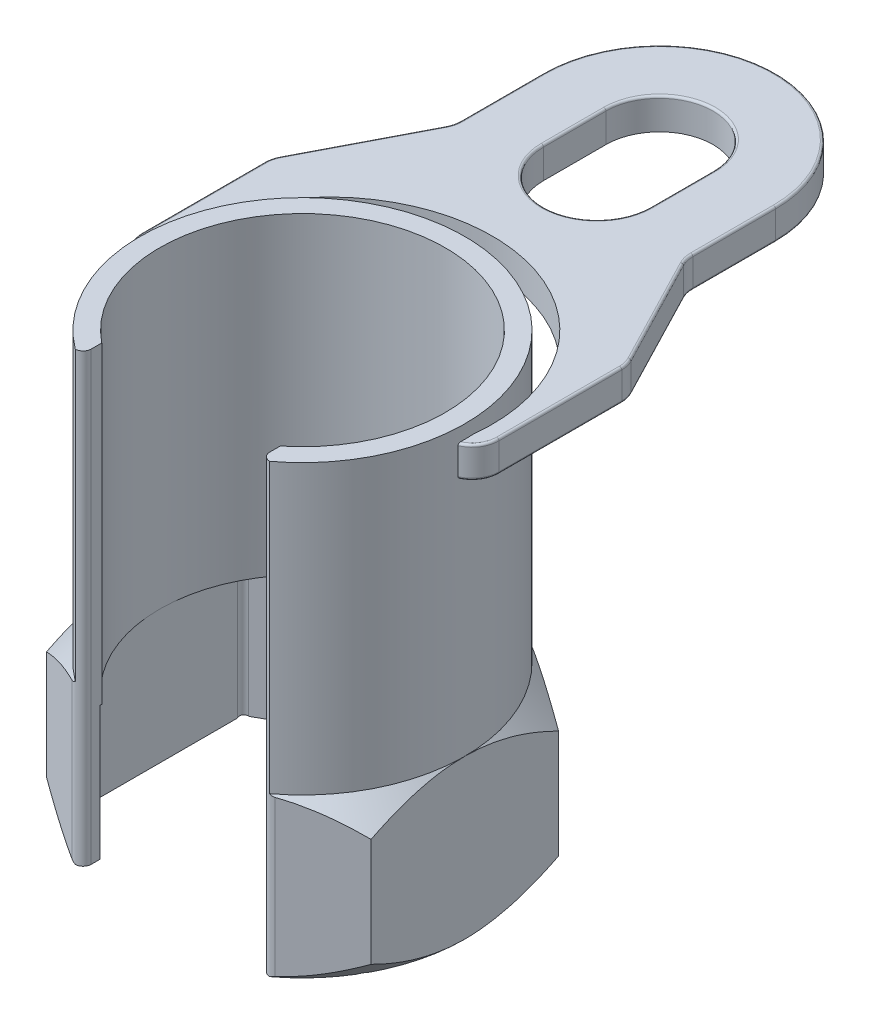
SolidWorks part; units mm, degrees
ref_plane "Front" through (0, 0, 0) normal (0, 0, 1) x (1, 0, 0)
ref_plane "Top" through (0, 0, 0) normal (0, 1, 0) x (1, 0, 0)
ref_plane "Right" through (0, 0, 0) normal (1, 0, 0) x (0, 0, -1)
sketch "Sketch1" plane through (0, 0, 0) normal (0, 1, 0) x (1, 0, 0)
  line L0 (-20, -24.98) -> (-20, -30.453)
  line L1 (0, 42) -> (-36.3731, 21)
  line L2 (0, 11.9615) -> (0, -7.933) construction
  line L3 (-36.3731, 21) -> (-36.3731, -21)
  line L4 (-36.3731, -21) -> (-20, -30.453)
  line L5 (20, -30.453) -> (36.3731, -21)
  line L6 (36.3731, -21) -> (36.3731, 21)
  line L7 (36.3731, 21) -> (0, 42)
  line L8 (20, -24.98) -> (20, -30.453)
  arc A0 (20, -30.3809) -> (-20, -30.3809) centre (0, 0) ccw construction
  arc A1 (20, -24.98) -> (-20, -24.98) centre (0, 0) ccw
  point P18 (-36.3731, -21)
  point P26 (36.3731, 21)
  dimension "D" = 84
  dimension "D2" = 64
  dimension "C" = 40
extrude "Extrude1" add sketch "Sketch1" along normal blind 35.5
sketch "Sketch3" plane through (0, 35.5, 0) normal (0, 1, 0) x (-1, 0, 0)
  line L0 (-36.3731, 21) -> (-36.3731, -21) construction
  line L2 (-20, 30.3808) -> (-20, 24.98)
  line L3 (20, 30.3808) -> (20, 24.98)
  arc A0 (-20, 24.98) -> (20, 24.98) centre (0, 0) ccw
  arc A1 (-20, 24.98) -> (20, 24.98) centre (0, 0) ccw construction
  arc A2 (-20, 30.3808) -> (20, 30.3808) centre (0, 0) ccw
  dimension "D1" = 0.0001
extrude "Extrude2" add sketch "Sketch3" along normal blind 64.5
sketch "Sketch8" plane through (0, 0, 0) normal (0, -1, 0) x (1, 0, 0)
  line L1 (36.3731, 21) -> (36.3731, -21) construction
  circle A0 centre (0, 0) radius 36.3731
extrude "Cut-Extrude4" cut sketch "Sketch8" against normal through all draft 45 flip side to cut
sketch "Sketch19" plane through (0, 35.5, 0) normal (0, 1, 0) x (-1, 0, 0)
  circle A1 centre (0, 0) radius 36.373
  arc A2 (-20, 30.3808) -> (20, 30.3808) centre (0, 0) ccw construction
extrude "Cut-Extrude6" cut sketch "Sketch19" against normal through all draft 45 flip side to cut
sketch "Sketch26" plane through (0, 0, 0) normal (0, -1, 0) x (1, 0, 0)
  line L1 (-32, -18.4752) -> (0, -36.9504)
  line L2 (0, -36.9504) -> (32, -18.4752)
  line L3 (32, -18.4752) -> (32, 18.4752)
  line L4 (32, 18.4752) -> (0, 36.9504)
  line L5 (0, 36.9504) -> (-32, 18.4752)
  line L6 (-32, 18.4752) -> (-32, -18.4752)
  circle A0 centre (0, 0) radius 32 construction
  dimension "D1" = 64
extrude "Cut-Extrude9" cut sketch "Sketch26" against normal up to vertex (38.5 mm away)
fillet "Fillet1" radius 1.8 7 edges at (-32, 15.2252, -18.4752) (-32, 15.2252, 18.4752) (32, 15.2252, 18.4752) (32, 15.2252, -18.4752) (-20, 17.7499, 30.453) (20, 17.7499, 30.453) (0, 15.2252, -36.9504)
sketch "Sketch4" [suppressed] plane through (0, 0, 0) normal (0, 1, 0) x (-1, 0, 0)
  line L0 (0, -11.2014) -> (0, 12.8888) construction
  line L1 (-10, -2.5) -> (10, -2.5)
  line L2 (-10, -2.5) -> (-10, 3.8)
  line L3 (-10, 3.8) -> (10, 3.8)
  line L4 (10, -2.5) -> (10, 3.8)
  line L5 (16.2585, 0) -> (-21.4153, 0) construction
  dimension "D1" = 64
  dimension "D2" = 11.5
  dimension "D3" = 10.2
sketch "Sketch12" [suppressed] plane through (0, 0, 0) normal (0, 1, 0) x (1, 0, 0)
  line L0 (-11, -4) -> (11, -4)
  line L1 (0, 0) -> (-11.4274, 0) construction
  line L2 (-11, 2.7) -> (11, 2.7)
  line L3 (-4.5, 14.3091) -> (4.5, 14.3091)
  line L4 (-7, 3.2909) -> (-7, -3.2909) construction
  line L5 (7, -3.2909) -> (7, 3.2909) construction
  arc A0 (-11, -4) -> (11, -4) centre (0, 0) ccw
  arc A1 (-6.3246, -3) -> (6.3246, -3) centre (0, 0) ccw construction
  arc A2 (-4.5, 14.3091) -> (-11, 2.7) centre (2.617, 2.7) ccw
  arc A3 (-4.5, 14.3091) -> (4.5, 14.3091) centre (0, 0) ccw construction
  arc A4 (4.5, 14.3091) -> (11, 2.7) centre (-2.617, 2.7) cw
ref_plane "Plane3" through (0, 90, 0) normal (0, 1, 0) x (-1, 0, 0)
sketch "Sketch16" plane through (0, 90, 0) normal (0, 1, 0) x (-1, 0, 0)
  line L5 (0, 0) -> (0, 54.2988) construction
  line L6 (-26, -80) -> (-26, -61.4631)
  line L10 (26, -61.4631) -> (26, -80)
  line L11 (39.3265, -34.2988) -> (26.6735, -58.7012)
  line L12 (-39.3265, -34.2988) -> (-26.6735, -58.7012)
  line L13 (-40, -4.024) -> (-40, -31.5369)
  line L14 (40, -4.024) -> (40, -31.5369)
  line L15 (38.3763, 1.5) -> (-38.1367, 1.5) construction
  arc A0 (-21.7747, 29.1351) -> (21.7747, 29.1351) centre (0, 0) ccw construction
  arc A1 (-36.342, 1.5) -> (36.342, 1.5) centre (0, 0) ccw
  arc A2 (40, -4.024) -> (36.342, 1.5) centre (34, -4.024) ccw
  arc A3 (-40, -4.024) -> (-36.342, 1.5) centre (-34, -4.024) cw
  arc A4 (-40, -31.5369) -> (-39.3265, -34.2988) centre (-34, -31.5369) ccw
  arc A5 (-26.6735, -58.7012) -> (-26, -61.4631) centre (-32, -61.4631) cw
  arc A7 (40, -31.5369) -> (39.3265, -34.2988) centre (34, -31.5369) cw
  arc A8 (26.6735, -58.7012) -> (26, -61.4631) centre (32, -61.4631) ccw
  arc A15 (26, -80) -> (-26, -80) centre (0, -80) cw
  point P18 (-40, -33)
  point P22 (-26, -60)
  point P25 (40, -33)
  point P30 (26, -60)
  dimension "D1" = 80
  dimension "D2" = 33
  dimension "D3" = 60
  dimension "D4" = 6
  dimension "D6" = 52
  dimension "D7" = 80
  dimension "D14" = 1.5
extrude "Extrude7" add sketch "Sketch16" along normal blind 7
sketch "Sketch25" plane through (0, 97, 0) normal (0, -1, 0) x (1, 0, 0)
  line L1 (-29.4486, 0) -> (37.9585, 0) construction
  line L3 (0, -57.3769) -> (0, 10.8445) construction
  line L4 (-12, -80) -> (-12, -66)
  line L5 (12, -80) -> (12, -66)
  arc A0 (-21.7747, 29.1351) -> (21.7747, 29.1351) centre (0, 0) ccw construction
  arc A2 (-26, -80) -> (26, -80) centre (0, -80) ccw construction
  arc A6 (36.3179, -2) -> (-36.3179, -2) centre (0, 0) cw
  arc A7 (36.3179, -2) -> (-36.3179, -2) centre (0, -6) cw
  arc A8 (12, -80) -> (-12, -80) centre (0, -80) cw
  arc A9 (12, -66) -> (-12, -66) centre (0, -66) ccw
  dimension "D1" = 40
  dimension "D2" = 24
  dimension "D3" = 2
  dimension "D4" = 6
extrude "Cut-Extrude8" cut sketch "Sketch25" along normal up to next
fillet "Fillet4" radius 0.5 30 edges at (12, 97, -73) (0, 97, -92) (-12, 97, -73) (39.0026, 97, -0.7113) (40, 97, -17.7805) (39.8292, 97, -32.9584) (-39.0026, 97, -0.7113) (-40, 97, -17.7805) (-39.8292, 97, -32.9584) (-33, 97, -46.5) (-26.1708, 97, -60.0416) (-26, 97, -70.7315) (0, 97, -106) (26, 97, -70.7315) (26.1708, 97, -60.0416) (39.0026, 90, -0.7113) (40, 90, -17.7805) (39.8292, 90, -32.9584) (-39.0026, 90, -0.7113) (-40, 90, -17.7805) (-39.8292, 90, -32.9584) (-33, 90, -46.5) (-26.1708, 90, -60.0416) (-26, 90, -70.7315) (0, 90, -106) (26, 90, -70.7315) (26.1708, 90, -60.0416) (0, 97, -54) (33, 97, -46.5) (33, 90, -46.5)
sketch "Sketch20" [suppressed] plane through (0, 0, 0) normal (0, 1, 0) x (1, 0, 0)
  line L0 (0, 0) -> (0, 12.8849) construction
  line L1 (-7.5, -9.3675) -> (-7.5, -14.4157)
  line L2 (7.5, -9.3675) -> (7.5, -14.4157)
  arc A0 (7.5, -14.4157) -> (-7.5, -14.4157) centre (0, 0) ccw
  arc A1 (7.5, -9.3675) -> (-7.5, -9.3675) centre (0, 0) ccw
  circle A2 centre (0, 0) radius 16.25 construction
  circle A3 centre (0, 0) radius 12 construction
  dimension "D1" = 84
  dimension "D2" = 64
  dimension "D3" = 40
extrude "Extrude3" [suppressed] add sketch "Sketch20" along normal blind 70
ref_plane "Plane7" [suppressed] through (0, 41.999, 0) normal (0, 1, 0) x (-1, 0, 0)
sketch "Sketch21" [suppressed] plane through (0, 41.999, 0) normal (0, 1, 0) x (-1, 0, 0)
  line L1 (2.5, 16.0565) -> (2.5, 19.8734)
  line L2 (7.5, 14.4157) -> (7.5, 9.3675) construction
  line L4 (7.5, 14.4157) -> (7.5, 18.5729)
  arc A1 (2.5, 16.0565) -> (7.5, 14.4157) centre (0, 0) ccw
  arc A2 (2.5, 19.8734) -> (7.5, 18.5729) centre (0, 0) ccw
  arc A3 (-7.5, 14.4157) -> (7.5, 14.4157) centre (0, 0) ccw construction
  dimension "D1" = 6.3
  dimension "D2" = 2.5
extrude "Extrude4" [suppressed] add sketch "Sketch21" against normal blind 20 separate body
ref_plane "Plane6" [suppressed] through (5.0421, 41.999, -19.385) normal (0.2517, 0, -0.9678) x (-0.9678, 0, -0.2517)
sketch "Sketch22" [suppressed] plane through (5.0421, 41.999, -19.385) normal (0.2517, 0, -0.9678) x (-0.9678, 0, -0.2517)
  line L0 (20.03, 0) -> (-20.03, 0) construction
  line L1 (0, 0) -> (0, 14.8678) construction
  line L2 (-3.2, -3.3) -> (3.2, -3.3)
  line L3 (-3.2, -3.3) -> (-3.2, -9.7)
  line L4 (-3.2, -9.7) -> (3.2, -9.7)
  line L5 (3.2, -3.3) -> (3.2, -9.7)
  line L7 (-18.9345, -6.5) -> (19.4735, -6.5) construction
  dimension "D1" = 12
  dimension "D2" = 10
  dimension "D3" = 12
extrude "Extrude5" [suppressed] add sketch "Sketch22" along normal blind 26 and the other way up to next
sketch "Sketch23" [suppressed] plane through (8.0628, 0, -30.9986) normal (0.2517, 0, -0.9678) x (-0.9678, 0, -0.2517)
  circle A0 centre (0, 35.499) radius 4.5255
extrude "Extrude6" [suppressed] add sketch "Sketch23" along normal blind 60 draft 2
dome "Dome1" [suppressed] faces to dome 1 distance 3 parameters "D1"=3
sketch "Sketch24" [suppressed] plane through (0, 0, 0) normal (0, -1, 0) x (1, 0, 0)
  line L2 (-12, 6.9282) -> (-12, -6.9282)
  line L3 (-12, -6.9282) -> (0, -13.8564)
  line L4 (0, -13.8564) -> (12, -6.9282)
  line L5 (12, -6.9282) -> (12, 6.9282)
  line L6 (12, 6.9282) -> (0, 13.8564)
  line L7 (0, 13.8564) -> (-12, 6.9282)
  circle A0 centre (0, 0) radius 12 construction
  dimension "D1" = 64
extrude "Cut-Extrude7" [suppressed] cut sketch "Sketch24" against normal through all
fillet "Fillet2" [suppressed] radius 0.5
fillet "Fillet3" [suppressed] radius 0.5
fillet "Fillet5" [suppressed] radius 1
